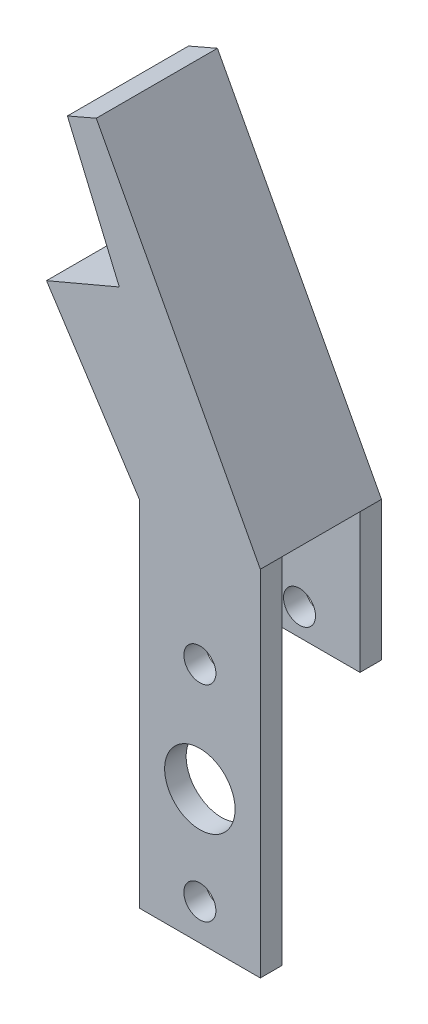
SolidWorks part; units mm, degrees
ref_plane "Front Plane" through (0, 0, 0) normal (0, 0, 1) x (1, 0, 0)
ref_plane "Top Plane" through (0, 0, 0) normal (0, 1, 0) x (1, 0, 0)
ref_plane "Right Plane" through (0, 0, 0) normal (1, 0, 0) x (0, 0, -1)
sketch "Sketch1" plane through (0, 0, 0) normal (0, 0, 1) x (1, 0, 0)
  line L0 (-1.5917, -17.7895) -> (12.7085, -17.7895)
  line L1 (12.7085, -17.7895) -> (12.7085, 24.0697)
  line L2 (12.7085, 24.0697) -> (-6.6928, 60.5582)
  line L3 (-1.5917, -17.7895) -> (-1.5917, 24.0697)
  line L4 (-1.5917, 24.0697) -> (-12.5758, 40.9837)
  line L5 (-12.5758, 40.9837) -> (-3.9716, 44.6359)
  line L6 (-3.9716, 44.6359) -> (-10.105, 59.0853)
  line L7 (-10.105, 59.0853) -> (-6.6928, 60.5582)
extrude "Boss-Extrude2" add sketch "Sketch1" along normal blind 14.3256
sketch "Sketch3" plane through (12.7085, 0, 0) normal (1, 0, 0) x (0, 0, -1)
  line L0 (-14.3256, -17.7895) -> (-11.7856, -17.7895)
  line L1 (-14.3256, -17.7895) -> (0, -17.7895) construction
  line L2 (-11.7856, -17.7895) -> (-11.7856, 24.0697)
  line L3 (-11.7856, 24.0697) -> (-2.54, 24.0697)
  line L4 (-2.54, 24.0697) -> (-2.54, -17.7895)
  line L5 (-2.54, -17.7895) -> (0, -17.7895)
  line L6 (0, -17.7895) -> (0, 24.0697)
  line L7 (0, 24.0697) -> (-14.3256, 24.0697)
  line L8 (-14.3256, 24.0697) -> (-14.3256, -17.7895)
  line L10 (-11.7856, 24.0697) -> (-2.54, 24.0697)
  line L11 (-11.7856, 24.0697) -> (-11.7856, -17.7895)
  line L12 (-11.7856, -17.7895) -> (-2.54, -17.7895)
  line L13 (-2.54, 24.0697) -> (-2.54, -17.7895)
  line M2 (0, 24.0697) -> (-14.3256, 24.0697)
  line M4 (-14.3256, -17.7895) -> (0, -17.7895)
extrude "Cut-Extrude1" cut sketch "Sketch3" against normal blind 14.3256 contours L4 L2 M2 M4
ref_plane "Plane1" through (12.7085, 24.0697, 11.7856) normal (0, 0, -1) x (-1, 0, 0)
sketch "Sketch5" plane through (12.7085, 0, 0) normal (1, 0, 0) x (0, 0, -1)
  line L0 (-2.54, 24.0697) -> (0, 24.0697)
  line L1 (0, 24.0697) -> (0, 7.6105)
  line L2 (0, -17.7895) -> (0, 24.0697) construction
  line L3 (0, 7.6105) -> (-2.54, 7.6105)
  line L4 (-2.54, 24.0697) -> (-2.54, -17.7895) construction
  line L6 (-2.54, 7.6105) -> (0, 7.6105)
  line L7 (-2.54, 7.6105) -> (-2.54, -17.7895)
  line L8 (-2.54, -17.7895) -> (0, -17.7895)
  line L9 (0, 7.6105) -> (0, -17.7895)
  line M1 (-2.54, 24.0697) -> (-2.54, -17.7895)
  line M2 (-2.54, -17.7895) -> (0, -17.7895)
  line M3 (0, -17.7895) -> (0, 24.0697)
extrude "Cut-Extrude2" cut sketch "Sketch5" against normal blind 14.3256 contours L3 M3 M1 M2
sketch "Sketch6" plane through (0, 0, 14.3256) normal (0, 0, 1) x (1, 0, 0)
  line L0 (5.5584, -17.7895) -> (5.5584, -13.5223) construction
  line L1 (-1.5917, -17.7895) -> (12.7085, -17.7895) construction
  line L2 (5.5584, -13.5223) -> (5.5584, -2.0161) construction
  line L3 (5.5584, -2.0161) -> (5.5584, 10.7601) construction
  line L4 (5.5584, 10.7601) -> (5.5584, 37.5171) construction
  line L5 (12.7085, 24.0697) -> (-6.6928, 60.5582) construction
  circle A0 centre (5.5584, -13.5223) radius 1.8923
  circle A1 centre (5.5584, 10.7601) radius 1.8923
  circle A2 centre (5.5584, -2.0161) radius 4.1656
extrude "Cut-Extrude3" cut sketch "Sketch6" against normal blind 14.3256
